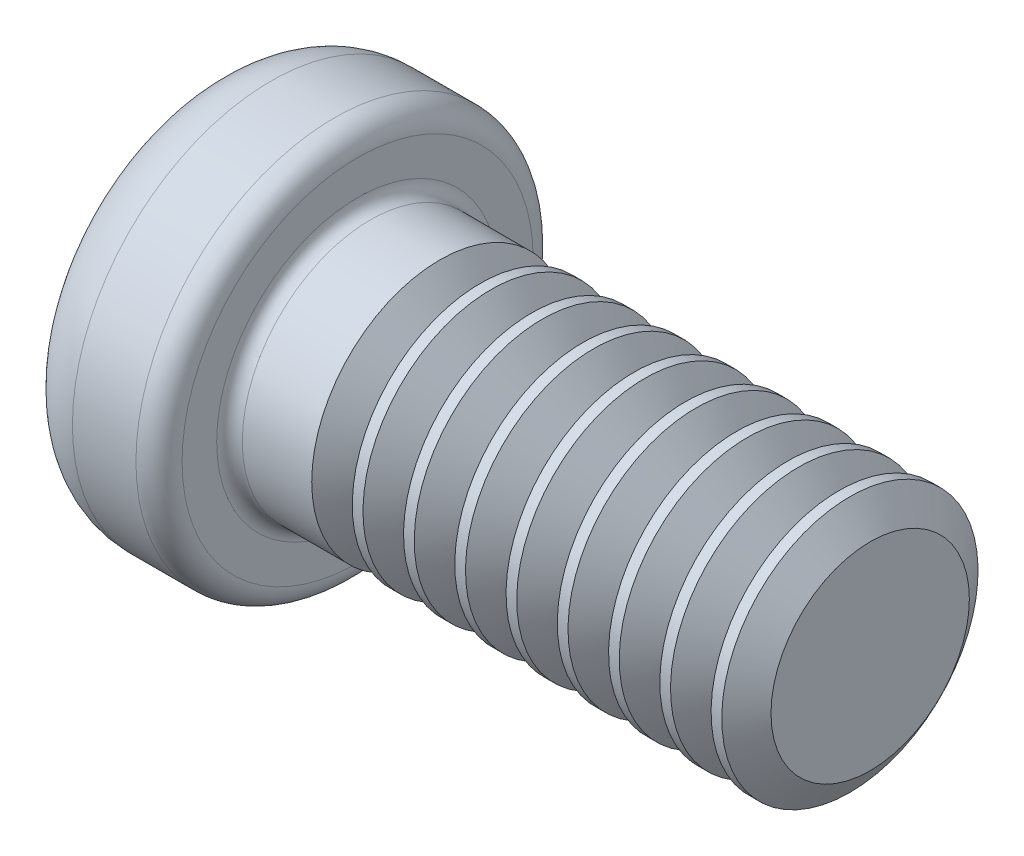
SolidWorks part; units mm, degrees
material "普通碳钢"
ref_plane "Plane1" through (0, 0, 0) normal (0, 0, 1) x (1, 0, 0)
ref_plane "Plane2" through (0, 0, 0) normal (0, 1, 0) x (1, 0, 0)
ref_plane "Plane3" through (0, 0, 0) normal (1, 0, 0) x (0, 0, -1)
sketch "BodySke" plane through (0, 0, 0) normal (0, 0, 1) x (1, 0, 0)
  line L0 (1.3, 1) -> (1.3, 1.37)
  line L1 (1.5, 6.35) -> (1.5, -3.175) construction
  line L2 (-25.4, 0) -> (127, 0) construction
  line L3 (5.3, 0) -> (0, 0)
  line L4 (1.3, 1) -> (5.3, 1)
  line L5 (5.3, 1) -> (5.3, 0)
  line L6 (0.6242, 1.55) -> (1.12, 1.55)
  line L8 (1.3, 6.35) -> (1.3, -3.175) construction
  arc A0 (0.138, 1.1667) -> (0, 0) centre (5, 0) ccw
  arc A1 (1.3, 1.37) -> (1.12, 1.55) centre (1.12, 1.37) ccw
  arc A2 (0.138, 1.1667) -> (0.6242, 1.55) centre (0.6242, 1.05) cw
  point P18 (1.3, 1.55)
  dimension "Head_crown_rad" = 5
  dimension "Head_fillet_rad" = 0.5
  dimension "D1" = 0.18
  dimension "Length" = 4
  dimension "Head_ht" = 1.3
  dimension "Head_dia" = 3.1
  dimension "Advance" = 0.4
  dimension "Thread_nom" = 4
  dimension "Diameter" = 2
revolve "Base-Revolve" add sketch "BodySke"
cosmetic thread "ThreadCosmetic" [suppressed]
fillet "Fillet1" radius 0.1 1 edges at (1.3, 0, 1)
sketch "Sketch3" plane through (0, 0, 0) normal (1, 0, 0) x (0, 0, -1)
  line L0 (0.24, -1.05) -> (-0.24, -1.05)
  line L1 (0.24, -1.05) -> (0.24, 1.05)
  line L2 (-0.24, 1.05) -> (0.24, 1.05)
  line L3 (-0.24, 1.05) -> (-0.24, -1.05)
  dimension "Cross_dia" = 2.1
  dimension "D1" = 1.05
  dimension "Cross_width" = 0.48
  dimension "D2" = 0.24
ref_plane "Plane4" through (1.42, 0, 0) normal (1, 0, 0) x (0, 0, -1)
sketch "Sketch4" plane through (1.42, 0, 0) normal (1, 0, 0) x (0, 0, -1)
  line L0 (0.24, -0.342) -> (-0.24, -0.342)
  line L1 (0.24, -0.342) -> (0.24, 0.342)
  line L2 (-0.24, 0.342) -> (0.24, 0.342)
  line L3 (-0.24, 0.342) -> (-0.24, -0.342)
  dimension "D1" = 0.48
  dimension "D2" = 0.684
  dimension "D3" = 0.24
  dimension "D4" = 0.342
loft "Recess" cut profiles "Sketch3", "Sketch4"
pattern_circular "RecPat" count 2 every 90 about axis through (0, 0, 0) along (1, 0, 0) of "Recess"
sketch "RecCorSke" plane through (0, 0, 0) normal (0, 0, 1) x (1, 0, 0)
  line L0 (-3.175, 0) -> (15.875, 0) construction
  line L1 (-25.4, 0) -> (127, 0) construction
  line L2 (0, 0) -> (0, 0.4548)
  line L3 (0, 0.4548) -> (1.42, 0.3555)
  line L4 (1.42, 0.3555) -> (1.5355, 0)
  line L5 (1.5355, 0) -> (0, 0)
  dimension "Diameter" = 0.711
  dimension "Depth" = 1.42
  dimension "Draft_angle" = 4
  dimension "Bottom_angle" = 18
revolve "RecessCore" cut sketch "RecCorSke" angle 360 about L0
sketch "ThdSchSke" plane through (0, 0, 0) normal (0, 0, 1) x (1, 0, 0)
  line L0 (2.1, -0.774) -> (1.9418, -1)
  line L1 (2.1, -0.774) -> (2.2582, -1)
  line L2 (2.2582, -1) -> (2.2582, -1.25)
  line L3 (-3.175, 0) -> (5.1513, 0) construction
  line L5 (2.2582, -1.25) -> (1.9418, -1.25)
  line L6 (1.9418, -1.25) -> (1.9418, -1)
  dimension "Diameter" = 2
  dimension "SideAngle" = 55
  dimension "VeeAngle" = 70
  dimension "Thread_minor" = 1.548
  dimension "Overcut" = 2.5
  dimension "Start" = 2.1
revolve "ThreadSchematic" cut sketch "ThdSchSke" angle 360 about L3
pattern_linear "ThdSchPat" count 9 spacing 0.4 along (1, 0, 0) of "ThreadSchematic"
equation "\"D1@Sketch3\" = \"Cross_dia@Sketch3\" / 2"
equation "\"D2@Sketch3\" = \"Cross_width@Sketch3\" / 2"
equation "\"Depth@RecCorSke\" = \"Cross_depth@Plane4\""
equation "\"D1@Sketch4\" = \"Cross_width@Sketch3\""
equation "\"D2@Sketch4\" = \"Cross_dia@Sketch3\" - 2.0 * \"Cross_depth@Plane4\" * tan(26.5  * 0.017453292)"
equation "\"D3@Sketch4\" = \"D1@Sketch4\" / 2"
equation "\"D4@Sketch4\" = \"D2@Sketch4\" / 2"
equation "\"Thread_length@ThreadCosmetic\" = ((sgn( (\"Length@BodySke\" - \"Advance@BodySke\" * 2.0 ) - \"Thread_nom@BodySke\" )-1)*( (\"Length@BodySke\" - \"Advance@BodySke\" * 2.0 ) - \"Thread_nom@BodySke\" ))/-2+ \"Thread_nom@BodySke\""
equation "\"Thread_minor@ThdSchSke\" = \"Thread_minor@ThreadCosmetic\""
equation "\"Diameter@ThdSchSke\" = \"Diameter@BodySke\""
equation "\"Overcut@ThdSchSke\" = \"Diameter@BodySke\" * 1.25"
equation "\"Start@ThdSchSke\" = \"Head_ht@BodySke\" + \"Length@BodySke\" - \"Thread_length@ThreadCosmetic\"  '---Non-countersunk---"
equation "\"Num_threads@ThdSchPat\" = int( \"Thread_length@ThreadCosmetic\" / \"Advance@BodySke\" + 0.999 )  + 1"
equation "\"Advance@ThdSchPat\" = \"Thread_length@ThreadCosmetic\" /  (\"Num_threads@ThdSchPat\" - 1) 'relax it"
